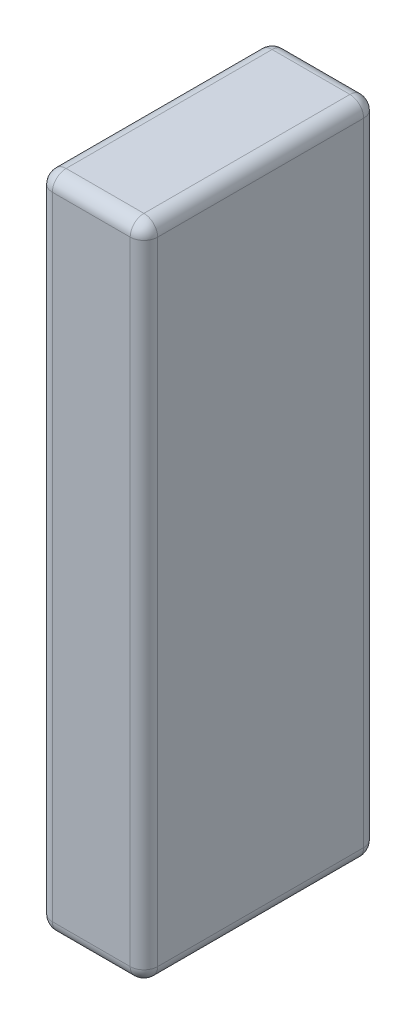
SolidWorks part; units mm, degrees
material "Lipo 3S"
ref_plane "Front Plane" through (0, 0, 0) normal (0, 0, 1) x (1, 0, 0)
ref_plane "Top Plane" through (0, 0, 0) normal (0, 1, 0) x (1, 0, 0)
ref_plane "Right Plane" through (0, 0, 0) normal (1, 0, 0) x (0, 0, -1)
sketch "Sketch1" plane through (0, 0, 0) normal (0, 1, 0) x (1, 0, 0)
  line L1 (0, 0) -> (23, 0)
  line L2 (0, 0) -> (0, 51)
  line L3 (0, 51) -> (23, 51)
  line L4 (23, 0) -> (23, 51)
  dimension "D1" = 51
  dimension "D2" = 23
extrude "Boss-Extrude1" add sketch "Sketch1" along normal blind 144
fillet "Fillet1" radius 3 12 edges at (11.5, 144, -51) (11.5, 0, -51) (0, 72, -51) (0, 144, -25.5) (0, 0, -25.5) (23, 144, -25.5) (23, 72, -51) (23, 0, -25.5) (0, 72, 0) (11.5, 144, 0) (23, 72, 0) (11.5, 0, 0)
